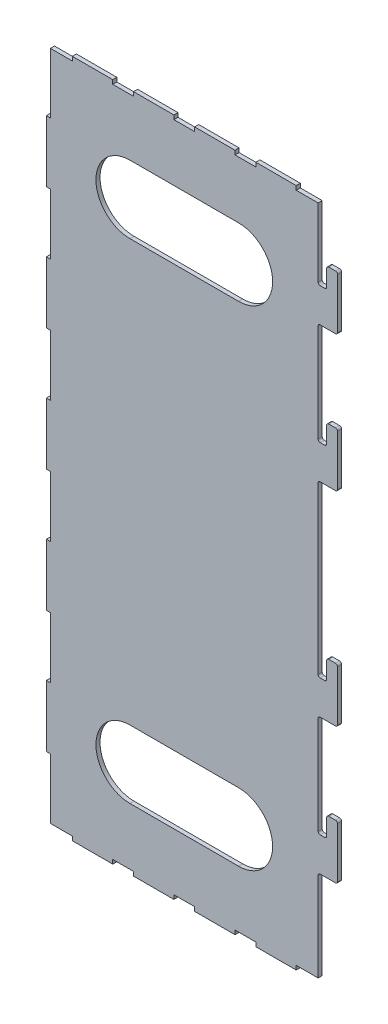
SolidWorks part; units mm, degrees
ref_plane "Alzado" through (0, 0, 0) normal (0, 0, 1) x (1, 0, 0)
ref_plane "Planta" through (0, 0, 0) normal (0, 1, 0) x (1, 0, 0)
ref_plane "Vista lateral" through (0, 0, 0) normal (1, 0, 0) x (0, 0, -1)
sketch "Croquis1" plane through (0, 0, 0) normal (0, 0, 1) x (1, 0, 0)
  line L0 (101.5, 195) -> (104.8, 195)
  line L1 (-100, 250) -> (100, 250)
  line L2 (-100, 250) -> (-100, -250)
  line L3 (-100, -250) -> (100, -250)
  line L4 (100, 250) -> (100, 196.5)
  line L5 (-100, 250) -> (100, -250) construction
  line L6 (-100, -250) -> (100, 250) construction
  line L7 (106.3, 196.5) -> (106.3, 208.5)
  line L8 (107.8, 210) -> (112.8, 210)
  line L9 (114.3, 208.5) -> (114.3, 171.5)
  line L10 (112.8, 170) -> (101.5, 170)
  line L11 (100, 168.5) -> (100, 96.5)
  line L12 (101.5, 95) -> (104.8, 95)
  line L13 (112.8, 70) -> (101.5, 70)
  line L14 (114.3, 108.5) -> (114.3, 71.5)
  line L15 (106.3, 96.5) -> (106.3, 108.5)
  line L16 (107.8, 110) -> (112.8, 110)
  line L22 (100, 68.5) -> (100, -53.5)
  line L24 (114.3, -30) -> (100, -30) [skipped]
  line L25 (114.3, 10) -> (114.3, -30) [skipped]
  line L26 (106.3, 10) -> (114.3, 10) [skipped]
  line L27 (106.3, -5) -> (106.3, 10) [skipped]
  line L28 (100, -5) -> (106.3, -5) [skipped]
  line L29 (0, 0) -> (-121.5606, 0) construction
  line L30 (101.5, -55) -> (104.8, -55)
  line L31 (106.3, -53.5) -> (106.3, -41.5)
  line L32 (107.8, -40) -> (112.8, -40)
  line L33 (114.3, -41.5) -> (114.3, -78.5)
  line L34 (112.8, -80) -> (101.5, -80)
  line L35 (101.5, -155) -> (104.8, -155)
  line L36 (112.8, -180) -> (101.5, -180)
  line L37 (114.3, -141.5) -> (114.3, -178.5)
  line L38 (106.3, -153.5) -> (106.3, -141.5)
  line L39 (107.8, -140) -> (112.8, -140)
  line L40 (100, -81.5) -> (100, -153.5)
  line L41 (100, -181.5) -> (100, -250)
  arc A0 (114.3, 171.5) -> (112.8, 170) centre (112.8, 171.5) cw
  arc A1 (112.8, 210) -> (114.3, 208.5) centre (112.8, 208.5) cw
  arc A2 (106.3, 208.5) -> (107.8, 210) centre (107.8, 208.5) cw
  arc A3 (104.8, 195) -> (106.3, 196.5) centre (104.8, 196.5) ccw
  arc A4 (101.5, 195) -> (100, 196.5) centre (101.5, 196.5) cw
  arc A5 (101.5, 170) -> (100, 168.5) centre (101.5, 168.5) ccw
  arc A6 (101.5, 70) -> (100, 68.5) centre (101.5, 68.5) ccw
  arc A7 (112.8, 70) -> (114.3, 71.5) centre (112.8, 71.5) ccw
  arc A8 (114.3, 108.5) -> (112.8, 110) centre (112.8, 108.5) ccw
  arc A9 (106.3, 108.5) -> (107.8, 110) centre (107.8, 108.5) cw
  arc A10 (104.8, 95) -> (106.3, 96.5) centre (104.8, 96.5) ccw
  arc A11 (101.5, 95) -> (100, 96.5) centre (101.5, 96.5) cw
  arc A12 (114.3, -78.5) -> (112.8, -80) centre (112.8, -78.5) cw
  arc A13 (112.8, -40) -> (114.3, -41.5) centre (112.8, -41.5) cw
  arc A14 (106.3, -41.5) -> (107.8, -40) centre (107.8, -41.5) cw
  arc A15 (104.8, -55) -> (106.3, -53.5) centre (104.8, -53.5) ccw
  arc A16 (101.5, -55) -> (100, -53.5) centre (101.5, -53.5) cw
  arc A17 (101.5, -80) -> (100, -81.5) centre (101.5, -81.5) ccw
  arc A18 (101.5, -180) -> (100, -181.5) centre (101.5, -181.5) ccw
  arc A19 (112.8, -180) -> (114.3, -178.5) centre (112.8, -178.5) ccw
  arc A20 (114.3, -141.5) -> (112.8, -140) centre (112.8, -141.5) ccw
  arc A21 (106.3, -141.5) -> (107.8, -140) centre (107.8, -141.5) cw
  arc A22 (104.8, -155) -> (106.3, -153.5) centre (104.8, -153.5) ccw
  arc A23 (101.5, -155) -> (100, -153.5) centre (101.5, -153.5) cw
  point P0 (0, 0)
  point P46 (100, 170)
  dimension "D10" = 1.5
  dimension "D11" = 1.5
  dimension "D12" = 1.5
  dimension "D1" = 500
  dimension "D2" = 200
  dimension "D3" = 6.3
  dimension "D4" = 8
  dimension "D5" = 40
  dimension "D6" = 40
  dimension "D7" = 25
  dimension "D9" = 60
  dimension "D14" = 110
  dimension "D8" = 3
  dimension "D13" = 2
extrude "Saliente-Extruir1" add sketch "Croquis1" along normal blind 3
sketch "Croquis2" plane through (0, 0, 3) normal (0, 0, 1) x (1, 0, 0)
  line L0 (100, 250) -> (100, 247)
  line L1 (100, -250) -> (100, -247)
  line L2 (41.5, 205) -> (-38.5, 205)
  line L3 (-38.5, 155) -> (41.5, 155)
  line L4 (41.5, 205) -> (-38.5, 205)
  line L5 (-38.5, 155) -> (41.5, 155)
  line L6 (-38.5, -205) -> (41.5, -205)
  line L7 (41.5, -155) -> (-38.5, -155)
  line L8 (-38.5, -205) -> (41.5, -205)
  line L9 (41.5, -155) -> (-38.5, -155)
  line L12 (-100, 250) -> (100, 250) construction
  line L14 (-100, 250) -> (-100, -250) construction
  line L17 (-100, -250) -> (100, -250)
  line L18 (-100, 250) -> (-100, -250)
  line L19 (100, 250) -> (-100, 250)
  line L64 (-6.15, -247) -> (9.15, -247)
  line L65 (9.15, -247) -> (9.15, -250)
  line L66 (9.15, -250) -> (38.85, -250)
  line L67 (38.85, -250) -> (38.85, -247)
  line L68 (38.85, -247) -> (54.15, -247)
  line L69 (54.15, -247) -> (54.15, -250)
  line L70 (54.15, -250) -> (83.85, -250)
  line L71 (83.85, -250) -> (83.85, -247)
  line L72 (83.85, -247) -> (100, -247)
  line L73 (100, -247) -> (100, 247)
  line L74 (100, 247) -> (83.85, 247)
  line L75 (83.85, 247) -> (83.85, 253)
  line L76 (83.85, 253) -> (54.15, 253)
  line L77 (54.15, 253) -> (54.15, 247)
  line L78 (54.15, 247) -> (38.85, 247)
  line L79 (38.85, 247) -> (38.85, 253)
  line L80 (38.85, 253) -> (9.15, 253)
  line L81 (9.15, 253) -> (9.15, 247)
  line L82 (9.15, 247) -> (-6.15, 247)
  line L83 (-6.15, 247) -> (-6.15, 253)
  line L84 (-6.15, 253) -> (-35.85, 253)
  line L85 (-35.85, 253) -> (-35.85, 247)
  line L86 (-35.85, 247) -> (-51.15, 247)
  line L87 (-51.15, 247) -> (-51.15, 253)
  line L88 (-51.15, 253) -> (-80.85, 253)
  line L89 (-80.85, 253) -> (-80.85, 247)
  line L90 (-80.85, 247) -> (-97, 247)
  line L91 (-97, 247) -> (-97, 202.65)
  line L92 (-97, 202.65) -> (-100, 202.65)
  line L93 (-100, 202.65) -> (-100, 157.35)
  line L94 (-100, 157.35) -> (-97, 157.35)
  line L95 (-97, 157.35) -> (-97, 112.65)
  line L96 (-97, 112.65) -> (-100, 112.65)
  line L97 (-100, 112.65) -> (-100, 67.35)
  line L98 (-100, 67.35) -> (-97, 67.35)
  line L99 (-97, 67.35) -> (-97, 22.65)
  line L100 (-97, 22.65) -> (-100, 22.65)
  line L101 (-100, 22.65) -> (-100, -22.65)
  line L102 (-100, -22.65) -> (-97, -22.65)
  line L103 (-97, -22.65) -> (-97, -67.35)
  line L104 (-97, -67.35) -> (-100, -67.35)
  line L105 (-100, -67.35) -> (-100, -112.65)
  line L106 (-100, -112.65) -> (-97, -112.65)
  line L107 (-97, -112.65) -> (-97, -157.35)
  line L108 (-97, -157.35) -> (-100, -157.35)
  line L109 (-100, -157.35) -> (-100, -202.65)
  line L110 (-100, -202.65) -> (-97, -202.65)
  line L111 (-97, -202.65) -> (-97, -247)
  line L112 (-97, -247) -> (-80.85, -247)
  line L113 (-80.85, -247) -> (-80.85, -250)
  line L114 (-80.85, -250) -> (-51.15, -250)
  line L115 (-51.15, -250) -> (-51.15, -247)
  line L116 (-51.15, -247) -> (-35.85, -247)
  line L117 (-35.85, -247) -> (-35.85, -250)
  line L118 (-35.85, -250) -> (-6.15, -250)
  line L119 (-6.15, -250) -> (-6.15, -247)
  line L120 (-6.15, -247) -> (9.15, -247)
  line L121 (9.15, -247) -> (9.15, -250)
  line L122 (9.15, -250) -> (38.85, -250)
  line L123 (38.85, -250) -> (38.85, -247)
  line L124 (38.85, -247) -> (54.15, -247)
  line L125 (54.15, -247) -> (54.15, -250)
  line L126 (54.15, -250) -> (83.85, -250)
  line L127 (83.85, -250) -> (83.85, -247)
  line L128 (83.85, -247) -> (100, -247)
  line L130 (100, 247) -> (83.85, 247)
  line L131 (83.85, 247) -> (83.85, 253)
  line L132 (83.85, 253) -> (54.15, 253)
  line L133 (54.15, 253) -> (54.15, 247)
  line L134 (54.15, 247) -> (38.85, 247)
  line L135 (38.85, 247) -> (38.85, 253)
  line L136 (38.85, 253) -> (9.15, 253)
  line L137 (9.15, 253) -> (9.15, 247)
  line L138 (9.15, 247) -> (-6.15, 247)
  line L139 (-6.15, 247) -> (-6.15, 253)
  line L140 (-6.15, 253) -> (-35.85, 253)
  line L141 (-35.85, 253) -> (-35.85, 247)
  line L142 (-35.85, 247) -> (-51.15, 247)
  line L143 (-51.15, 247) -> (-51.15, 253)
  line L144 (-51.15, 253) -> (-80.85, 253)
  line L145 (-80.85, 253) -> (-80.85, 247)
  line L146 (-80.85, 247) -> (-97, 247)
  line L147 (-97, 247) -> (-97, 202.65)
  line L148 (-97, 202.65) -> (-100, 202.65)
  line L149 (-100, 202.65) -> (-100, 157.35)
  line L150 (-100, 157.35) -> (-97, 157.35)
  line L151 (-97, 157.35) -> (-97, 112.65)
  line L152 (-97, 112.65) -> (-100, 112.65)
  line L153 (-100, 112.65) -> (-100, 67.35)
  line L154 (-100, 67.35) -> (-97, 67.35)
  line L155 (-97, 67.35) -> (-97, 22.65)
  line L156 (-97, 22.65) -> (-100, 22.65)
  line L157 (-100, 22.65) -> (-100, -22.65)
  line L158 (-100, -22.65) -> (-97, -22.65)
  line L159 (-97, -22.65) -> (-97, -67.35)
  line L160 (-97, -67.35) -> (-100, -67.35)
  line L161 (-100, -67.35) -> (-100, -112.65)
  line L162 (-100, -112.65) -> (-97, -112.65)
  line L163 (-97, -112.65) -> (-97, -157.35)
  line L164 (-97, -157.35) -> (-100, -157.35)
  line L165 (-100, -157.35) -> (-100, -202.65)
  line L166 (-100, -202.65) -> (-97, -202.65)
  line L167 (-97, -202.65) -> (-97, -247)
  line L168 (-97, -247) -> (-80.85, -247)
  line L169 (-80.85, -247) -> (-80.85, -250)
  line L170 (-80.85, -250) -> (-51.15, -250)
  line L171 (-51.15, -250) -> (-51.15, -247)
  line L172 (-51.15, -247) -> (-35.85, -247)
  line L173 (-35.85, -247) -> (-35.85, -250)
  line L174 (-35.85, -250) -> (-6.15, -250)
  line L175 (-6.15, -250) -> (-6.15, -247)
  line L826 (-100, -250) -> (100, -250) construction
  line L2568 (100, 247) -> (100, -247)
  arc A3 (-38.5, 205) -> (-38.5, 155) centre (-38.5, 180) ccw
  arc A4 (41.5, 155) -> (66.5, 180) centre (41.5, 180) ccw
  arc A5 (66.5, 180) -> (41.5, 205) centre (41.5, 180) ccw
  arc A6 (-38.5, 205) -> (-38.5, 155) centre (-38.5, 180) ccw
  arc A7 (41.5, 155) -> (66.5, 180) centre (41.5, 180) ccw
  arc A8 (66.5, 180) -> (41.5, 205) centre (41.5, 180) ccw
  arc A9 (41.5, -205) -> (66.5, -180) centre (41.5, -180) ccw
  arc A10 (-38.5, -155) -> (-38.5, -205) centre (-38.5, -180) ccw
  arc A11 (66.5, -180) -> (41.5, -155) centre (41.5, -180) ccw
  arc A12 (41.5, -205) -> (66.5, -180) centre (41.5, -180) ccw
  arc A13 (-38.5, -155) -> (-38.5, -205) centre (-38.5, -180) ccw
  arc A14 (66.5, -180) -> (41.5, -155) centre (41.5, -180) ccw
  dimension "D1" = 0
  dimension "D2" = 0
  dimension "D3" = 0
extrude "Cortar-Extruir1" cut sketch "Croquis2" against normal up to next
